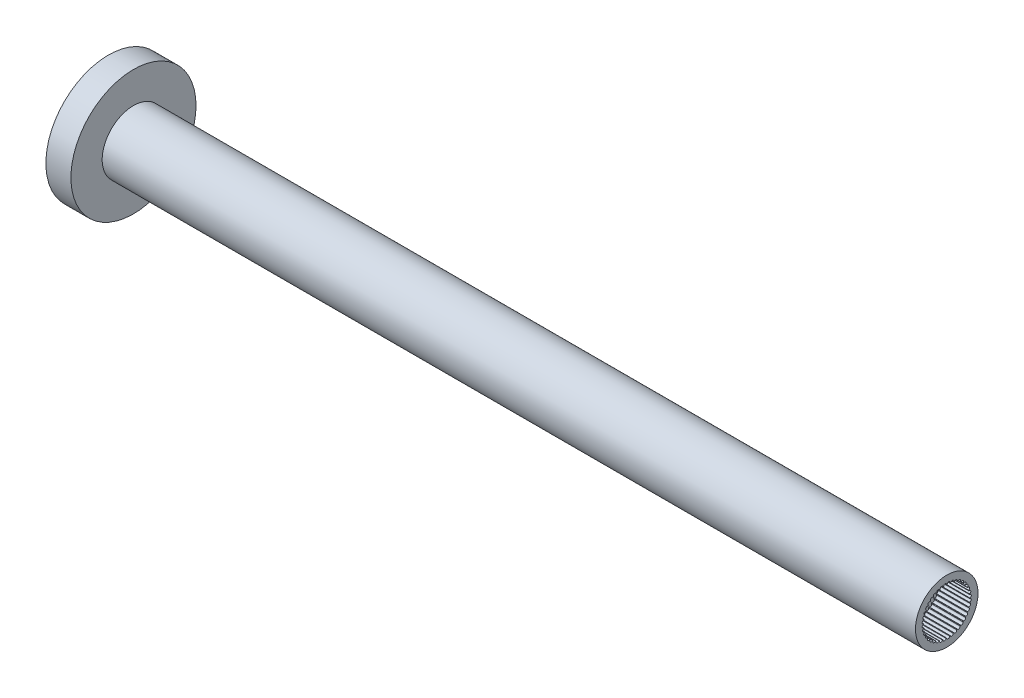
SolidWorks part; units mm, degrees
ref_plane "Front Plane" through (0, 0, 0) normal (0, 0, 1) x (1, 0, 0)
ref_plane "Top Plane" through (0, 0, 0) normal (0, 1, 0) x (1, 0, 0)
ref_plane "Right Plane" through (0, 0, 0) normal (1, 0, 0) x (0, 0, -1)
sketch "Sketch1" plane through (0, 0, 0) normal (1, 0, 0) x (0, 0, -1)
  circle A0 centre (0, 0) radius 6.35
  dimension "D1" = 12.7
extrude "Boss-Extrude1" add sketch "Sketch1" along normal blind 2.54
sketch "Sketch2" plane through (2.54, 0, 0) normal (1, 0, 0) x (0, 0, -1)
  circle A0 centre (0, 0) radius 3.175
  dimension "D1" = 6.35
extrude "Boss-Extrude2" add sketch "Sketch2" along normal blind 82.55
sketch "Sketch3" plane through (85.09, 0, 0) normal (1, 0, 0) x (0, 0, -1)
  circle A0 centre (0, 0) radius 2.3495
  point P85 (0, 0)
extrude "Cut-Extrude1" cut sketch "Sketch3" against normal blind 3.175
sketch "Sketch4" plane through (85.09, 0, 0) normal (1, 0, 0) x (0, 0, -1)
  circle A0 centre (0, 0) radius 2.3495 construction
  circle A1 centre (0, 0) radius 2.3495 construction
  circle A2 centre (1.2613, 1.9822) radius 0.1524
  circle A3 centre (1.5559, 1.7605) radius 0.1524
  circle A4 centre (1.8121, 1.4955) radius 0.1524
  circle A5 centre (2.0237, 1.1936) radius 0.1524
  circle A6 centre (2.1855, 0.8623) radius 0.1524
  circle A7 centre (2.2935, 0.5098) radius 0.1524
  circle A8 centre (2.345, 0.1447) radius 0.1524
  circle A9 centre (2.3388, -0.2239) radius 0.1524
  circle A10 centre (2.275, -0.587) radius 0.1524
  circle A11 centre (2.1551, -0.9357) radius 0.1524
  circle A12 centre (1.9822, -1.2613) radius 0.1524
  circle A13 centre (1.7605, -1.5559) radius 0.1524
  circle A14 centre (1.4955, -1.8121) radius 0.1524
  circle A15 centre (1.1936, -2.0237) radius 0.1524
  circle A16 centre (0.8623, -2.1855) radius 0.1524
  circle A17 centre (0.5098, -2.2935) radius 0.1524
  circle A18 centre (0.1447, -2.345) radius 0.1524
  circle A19 centre (-0.2239, -2.3388) radius 0.1524
  circle A20 centre (-0.587, -2.275) radius 0.1524
  circle A21 centre (-0.9357, -2.1551) radius 0.1524
  circle A22 centre (-1.2613, -1.9822) radius 0.1524
  circle A23 centre (-1.5559, -1.7605) radius 0.1524
  circle A24 centre (-1.8121, -1.4955) radius 0.1524
  circle A25 centre (-2.0237, -1.1936) radius 0.1524
  circle A26 centre (-2.1855, -0.8623) radius 0.1524
  circle A27 centre (-2.2935, -0.5098) radius 0.1524
  circle A28 centre (-2.345, -0.1447) radius 0.1524
  circle A29 centre (-2.3388, 0.2239) radius 0.1524
  circle A30 centre (-2.275, 0.587) radius 0.1524
  circle A31 centre (-2.1551, 0.9357) radius 0.1524
  circle A32 centre (-1.9822, 1.2613) radius 0.1524
  circle A33 centre (-1.7605, 1.5559) radius 0.1524
  circle A34 centre (-1.4955, 1.8121) radius 0.1524
  circle A35 centre (-1.1936, 2.0237) radius 0.1524
  circle A36 centre (-0.8623, 2.1855) radius 0.1524
  circle A37 centre (-0.5098, 2.2935) radius 0.1524
  circle A38 centre (-0.1447, 2.345) radius 0.1524
  circle A39 centre (0.2239, 2.3388) radius 0.1524
  circle A40 centre (0.587, 2.275) radius 0.1524
  circle A41 centre (0.9357, 2.1551) radius 0.1524
  point P85 (0, 0)
extrude "Cut-Extrude2" cut sketch "Sketch4" against normal blind 3.175
